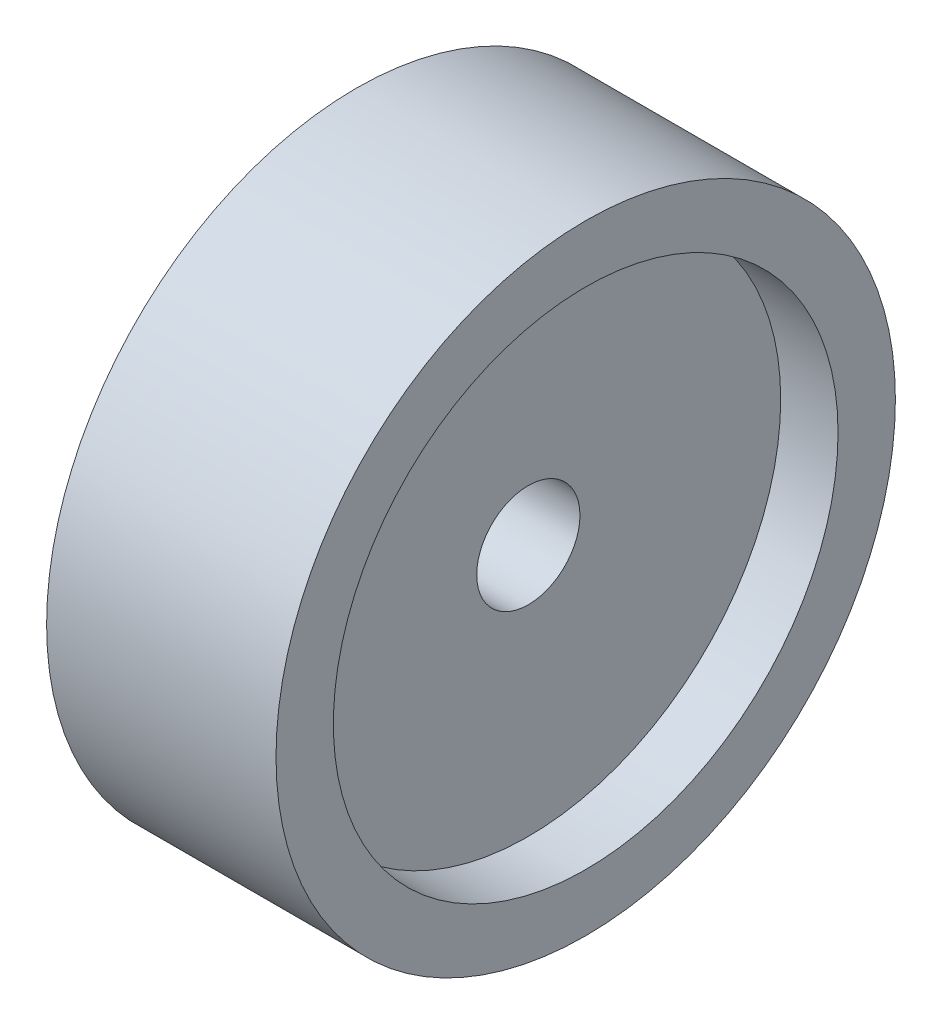
SolidWorks part; units mm, degrees
ref_plane "Plan de face" through (0, 0, 0) normal (0, 0, 1) x (1, 0, 0)
ref_plane "Plan de dessus" through (0, 0, 0) normal (0, 1, 0) x (1, 0, 0)
ref_plane "Plan de droite" through (0, 0, 0) normal (1, 0, 0) x (0, 0, -1)
sketch "Esquisse1" plane through (0, 0, 0) normal (1, 0, 0) x (0, 0, -1)
  circle A0 centre (0, 0) radius 27
  circle A1 centre (0, 0) radius 4.5
  dimension "D1" = 54
  dimension "D2" = 9
extrude "Extrusion1" add sketch "Esquisse1" along normal blind 20
sketch "Esquisse2" plane through (0, 0, 0) normal (-1, 0, 0) x (0, 0, 1)
  circle A0 centre (0, 0) radius 22
  dimension "D1" = 44
extrude "Enlèv. mat.-Extru.1" cut sketch "Esquisse2" against normal blind 3
sketch "Esquisse3" plane through (20, 0, 0) normal (1, 0, 0) x (0, 0, -1)
  circle A0 centre (0, 0) radius 22
  dimension "D1" = 44
extrude "Enlèv. mat.-Extru.2" cut sketch "Esquisse3" against normal blind 5
